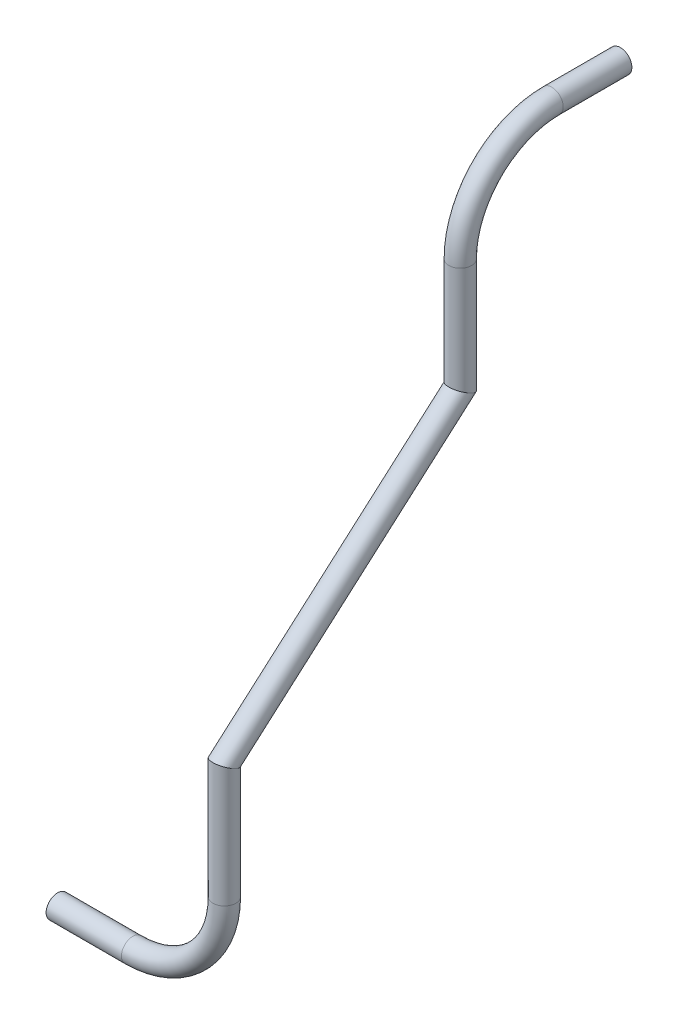
SolidWorks part; units mm, degrees
ref_plane "Front Plane" through (0, 0, 0) normal (0, 0, 1) x (1, 0, 0)
ref_plane "Top Plane" through (0, 0, 0) normal (0, 1, 0) x (1, 0, 0)
ref_plane "Right Plane" through (0, 0, 0) normal (1, 0, 0) x (0, 0, -1)
sketch3d "3DSketch1"
  line L0 (-402.7857, 1382.2439, 528.6756) -> (-360.9906, 1382.2439, 528.6756)
  line L1 (-310.1906, 1433.0439, 528.6756) -> (-310.1906, 1497.7788, 528.6756)
  line L2 (-310.1906, 1497.7788, 528.6756) -> (-310.201, 1612.8456, 397.7022)
  line L3 (-310.201, 1612.8456, 397.7022) -> (-310.201, 1674.1572, 397.7022)
  line L5 (-310.201, 1724.9572, 346.9022) -> (-310.201, 1724.9572, 308.8022)
  circle A2 centre (-402.7857, 1382.2439, 528.6756) radius 8.0124 construction
  circle A3 centre (-310.201, 1724.9572, 308.8022) radius 8.0124 construction
  arc A5 (-310.201, 1674.1572, 397.7022) -> (-310.201, 1724.9572, 346.9022) centre (-310.201, 1674.1572, 346.9022) ccw
  arc A6 (-360.9906, 1382.2439, 528.6756) -> (-310.1906, 1433.0439, 528.6756) centre (-360.9906, 1433.0439, 528.6756) ccw
  point P6 (-394.7732, 1382.2439, 528.6756)
  point P12 (-310.201, 1724.9572, 300.7898)
  point P25 (-310.201, 1724.9572, 397.7022)
  point P27 (-361.001, 1674.1572, 346.9022)
  point P32 (-310.1906, 1382.2439, 528.6756)
  point P33 (-360.9906, 1433.0439, 579.4756)
  dimension "D1" = 50.8
  dimension "D2" = 50.8
  dimension "D3" = 38.1
other "Pipe 0.5 SCH 40(1)"
ref_plane "Plane1" through (-402.7857, 1382.2439, 528.6756) normal (1, 0, 0) x (0, 0, -1)
sketch "Sketch1" plane through (-402.7857, 1382.2439, 528.6756) normal (1, 0, 0) x (0, 0, -1)
  circle A0 centre (0, 0) radius 5.2832
  circle A1 centre (0, 0) radius 6.35
  point P5 (0, 0)
  dimension "In_dia" = 10.5664
  dimension "Out_dia" = 12.7
